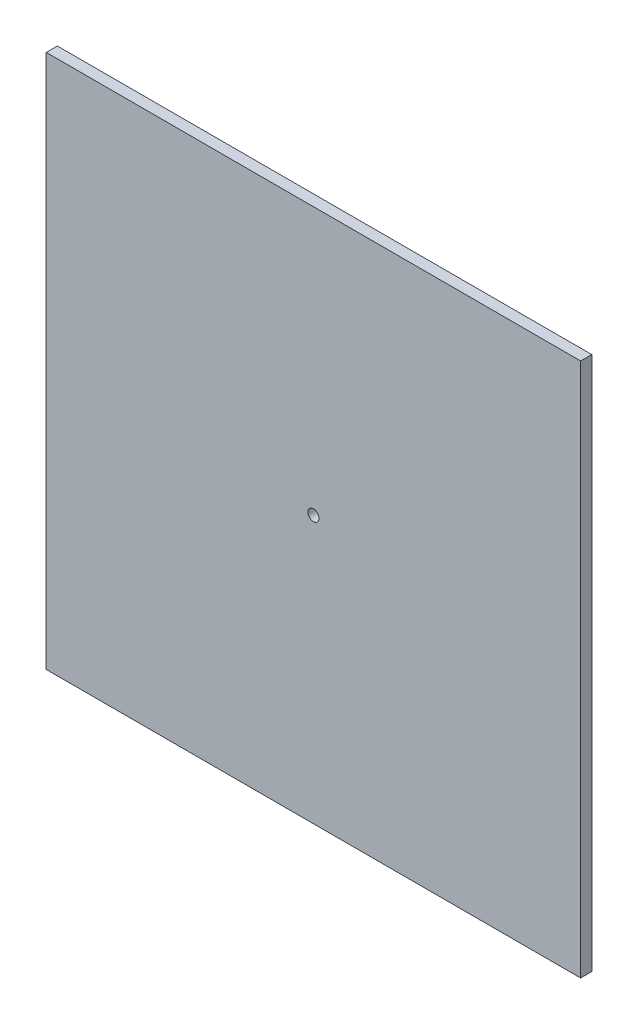
SolidWorks part; units mm, degrees
material "Oak"
ref_plane "Front Plane" through (0, 0, 0) normal (0, 0, 1) x (1, 0, 0)
ref_plane "Top Plane" through (0, 0, 0) normal (0, 1, 0) x (1, 0, 0)
ref_plane "Right Plane" through (0, 0, 0) normal (1, 0, 0) x (0, 0, -1)
sketch "Sketch1" plane through (0, 0, 0) normal (0, 0, 1) x (1, 0, 0)
  line L1 (0, 0) -> (-304.8, 0)
  line L2 (0, 0) -> (0, 304.8)
  line L3 (0, 304.8) -> (-304.8, 304.8)
  line L4 (-304.8, 0) -> (-304.8, 304.8)
  dimension "D1" = 304.8
  dimension "D2" = 304.8
extrude "Boss-Extrude1" add sketch "Sketch1" along normal blind 6.35
hole_wizard "1/4 (0.25) Diameter Hole1" positions "Sketch2" profile "Sketch3" hole size "1/4" standard "ANSI Inch"
sketch "Sketch2" plane through (0, 0, 6.35) normal (0, 0, 1) x (1, 0, 0)
  line L0 (-152.4, 0) -> (-152.4, 304.8) construction
  line L1 (0.4353, 152.4) -> (-305.2353, 152.4) construction
  line L2 (0, 304.8) -> (-304.8, 304.8) construction
  line L3 (-304.8, 0) -> (0, 0) construction
  point P0 (-152.4, 152.4)
sketch "Sketch3" plane through (-152.4, 152.4, 6.35) normal (1, 0, 0) x (0, -1, 0)
  line L0 (0, 0) -> (0, 8.2567)
  line L1 (0, 8.2567) -> (3.175, 6.349)
  line L2 (3.175, 6.349) -> (3.175, 0)
  line L5 (3.175, 0) -> (0, 0)
  line L10 (0, 8.2567) -> (-3.175, 6.349) construction
  line L11 (0, -6.35) -> (0, 107.95) construction
  dimension "Hole Dia." = 6.35
  dimension "Hole Depth" = 6.349
  dimension "Drill Angle" = 118
